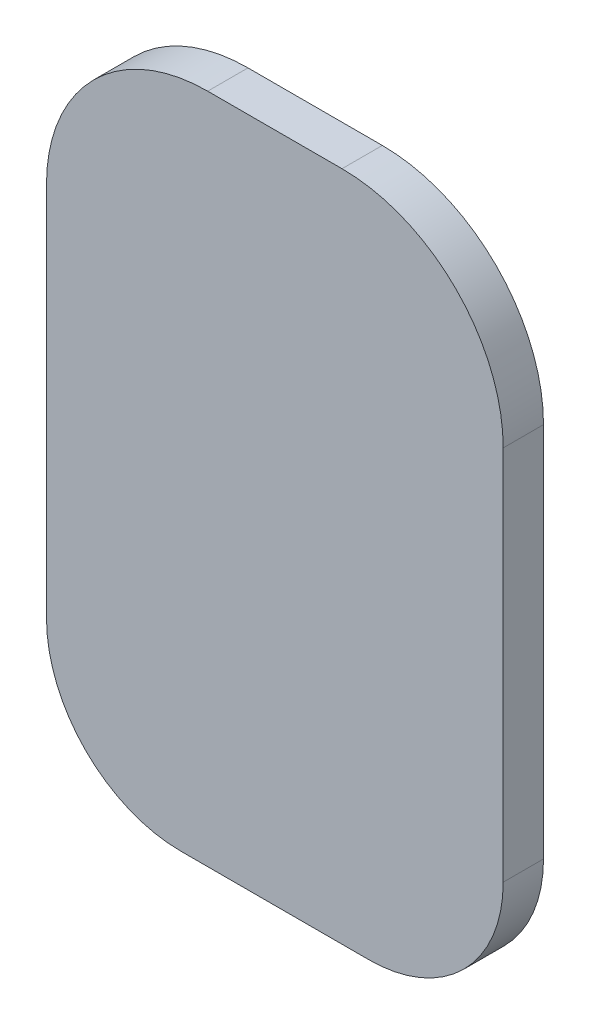
SolidWorks part; units mm, degrees
ref_plane "Front Plane" through (0, 0, 0) normal (0, 0, 1) x (1, 0, 0)
ref_plane "Top Plane" through (0, 0, 0) normal (0, 1, 0) x (1, 0, 0)
ref_plane "Right Plane" through (0, 0, 0) normal (1, 0, 0) x (0, 0, -1)
sketch "Sketch1" plane through (0, 0, 0) normal (0, 0, 1) x (1, 0, 0)
  line L0 (0, -21.5) -> (0, -71.5) construction
  line L1 (-17, -21.5) -> (17, -21.5) construction
  line L2 (-17, -21.5) -> (-17, -71.5) construction
  line L3 (-17, -71.5) -> (17, -71.5) construction
  line L4 (17, -21.5) -> (17, -71.5) construction
  line L5 (-5, -21.5) -> (5, -21.5)
  line L6 (-7, -71.5) -> (7, -71.5) construction
  line L7 (-17, -33.5) -> (17, -33.5) construction
  line L8 (-17, -33.5) -> (-17, -61.5)
  line L9 (-17, -61.5) -> (17, -61.5) construction
  line L10 (17, -33.5) -> (17, -61.5)
  line L11 (-0.5, -71.5) -> (0.5, -71.5) construction
  line L12 (-7, -71.5) -> (-0.5, -71.5)
  line L13 (0.5, -71.5) -> (7, -71.5)
  line L14 (-0.5, -71.5) -> (0.5, -71.5)
  arc A0 (-17, -33.5) -> (-5, -21.5) centre (-5, -33.5) cw
  arc A1 (5, -21.5) -> (17, -33.5) centre (5, -33.5) cw
  arc A2 (-17, -61.5) -> (-7, -71.5) centre (-7, -61.5) ccw
  arc A3 (7, -71.5) -> (17, -61.5) centre (7, -61.5) ccw
  point P10 (0, -21.5)
  point P19 (0, -71.5)
  point P23 (0, -71.5)
  point P24 (32.2937, 37.3696)
  point P26 (0, -5.3385)
  dimension "D3" = 12
  dimension "D4" = 10
  dimension "D1" = 50
  dimension "D2" = 34
  dimension "D5" = 1
  dimension "D6" = 21.5
extrude "Boss-Extrude1" add sketch "Sketch1" along normal blind 3
